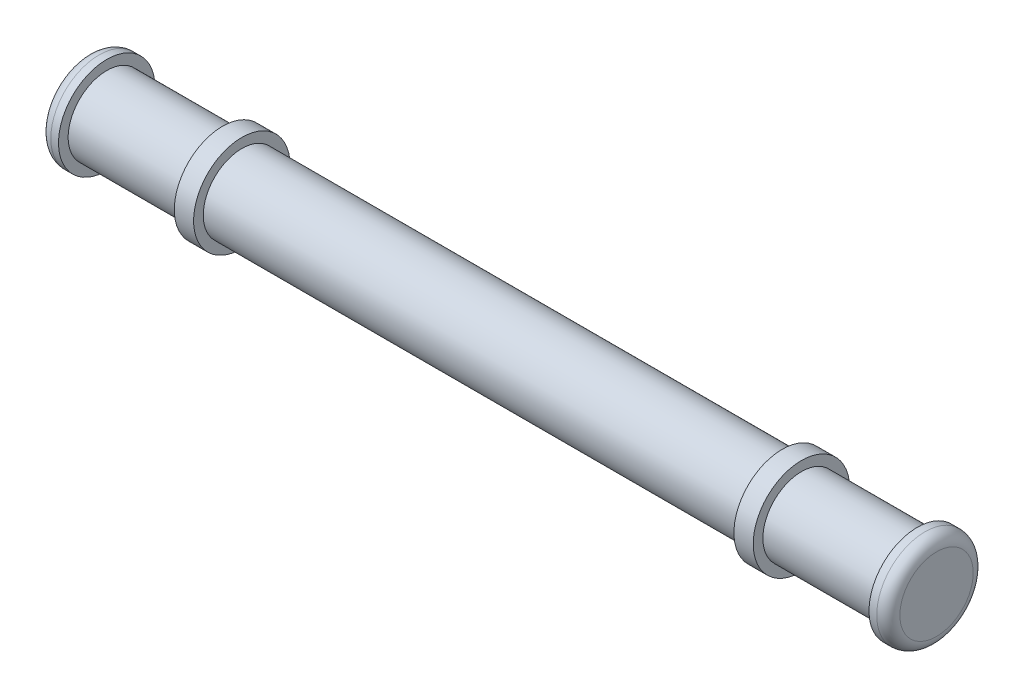
SolidWorks part; units mm, degrees
material "ABS"
ref_plane "Front Plane" through (0, 0, 0) normal (0, 0, 1) x (1, 0, 0)
ref_plane "Top Plane" through (0, 0, 0) normal (0, 1, 0) x (1, 0, 0)
ref_plane "Right Plane" through (0, 0, 0) normal (1, 0, 0) x (0, 0, -1)
sketch "Sketch1" plane through (0, 0, 0) normal (1, 0, 0) x (0, 0, -1)
  circle A0 centre (0, 0) radius 25.4
  dimension "D1" = 50.8
extrude "Boss-Extrude1" add sketch "Sketch1" along normal blind 355.6
sketch "Sketch2" plane through (355.6, 0, 0) normal (1, 0, 0) x (0, 0, -1)
  circle A0 centre (0, 0) radius 31.75
  dimension "D1" = 63.5
extrude "Boss-Extrude2" add sketch "Sketch2" along normal blind 12.7
sketch "Sketch3" plane through (368.3, 0, 0) normal (1, 0, 0) x (0, 0, -1)
  circle A0 centre (0, 0) radius 25.4
  dimension "D1" = 50.8
extrude "Boss-Extrude3" add sketch "Sketch3" along normal blind 76.2
sketch "Sketch4" plane through (444.5, 0, 0) normal (1, 0, 0) x (0, 0, -1)
  circle A0 centre (0, 0) radius 31.75
extrude "Boss-Extrude4" add sketch "Sketch4" along normal blind 12.7
ref_plane "Plane1" through (177.8, 0, 0) normal (-1, 0, 0) x (0, 0, 1)
mirror "Mirror1" about plane through (177.8, 0, 0) normal (-1, 0, 0) of "Boss-Extrude2", "Boss-Extrude3", "Boss-Extrude4"
fillet "Fillet1" radius 7.62 1 edges at (457.2, 0, -31.75)
fillet "Fillet2" radius 7.62 1 edges at (-101.6, 0, -31.75)
